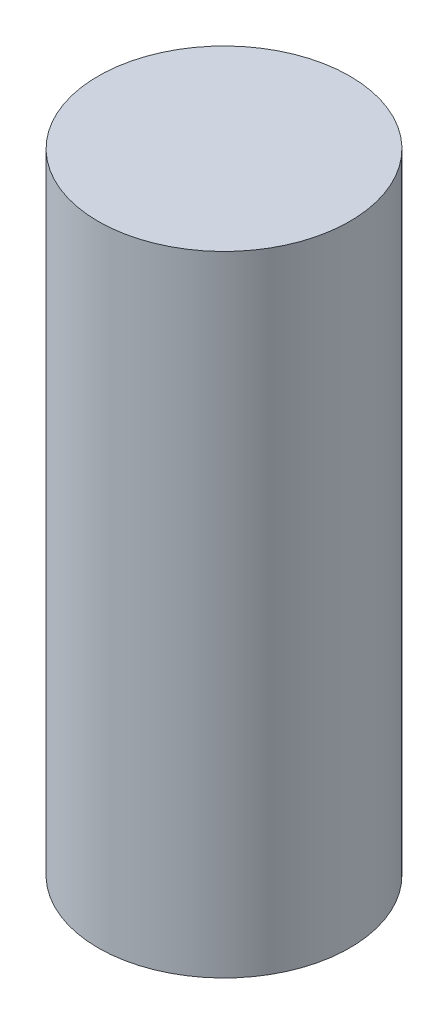
SolidWorks part; units mm, degrees
ref_plane "Front Plane" through (0, 0, 0) normal (0, 0, 1) x (1, 0, 0)
ref_plane "Top Plane" through (0, 0, 0) normal (0, 1, 0) x (1, 0, 0)
ref_plane "Right Plane" through (0, 0, 0) normal (1, 0, 0) x (0, 0, -1)
sketch "Sketch1" plane through (0, 0, 0) normal (0, 0, 1) x (1, 0, 0)
  line L1 (0, 0) -> (1.4, 0)
  line L4 (1.4, 0) -> (1.4, 7)
  line L10 (0, 0) -> (0, 7)
  line L11 (0, 7) -> (1.4, 7)
  dimension "D1" = 7
  dimension "D2" = 1.4
revolve "Revolve1" add sketch "Sketch1" angle 360 about L10
